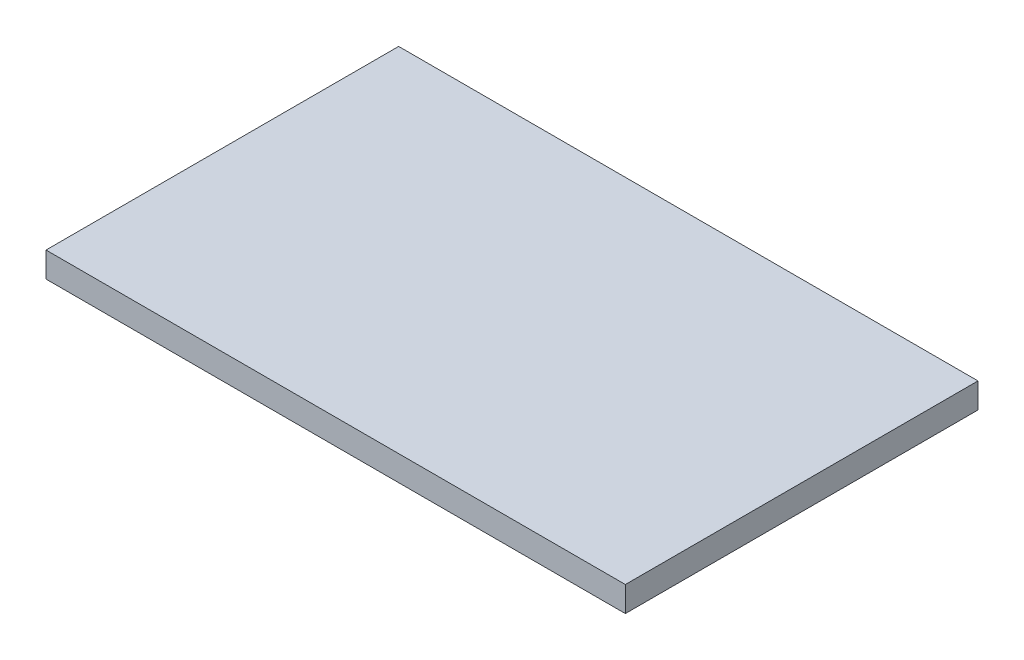
SolidWorks part; units mm, degrees
ref_plane "Front Plane" through (0, 0, 0) normal (0, 0, 1) x (1, 0, 0)
ref_plane "Top Plane" through (0, 0, 0) normal (0, 1, 0) x (1, 0, 0)
ref_plane "Right Plane" through (0, 0, 0) normal (1, 0, 0) x (0, 0, -1)
sketch "Sketch1" plane through (0, 0, 0) normal (0, 1, 0) x (1, 0, 0)
  line L1 (-584.2, -355.6) -> (584.2, -355.6)
  line L2 (-584.2, -355.6) -> (-584.2, 355.6)
  line L3 (-584.2, 355.6) -> (584.2, 355.6)
  line L4 (584.2, -355.6) -> (584.2, 355.6)
  line L5 (-584.2, -355.6) -> (584.2, 355.6) construction
  line L6 (-584.2, 355.6) -> (584.2, -355.6) construction
  point P0 (0, 0)
  dimension "D1" = 1168.4
  dimension "D2" = 711.2
extrude "Boss-Extrude1" add sketch "Sketch1" along normal blind 50.8
